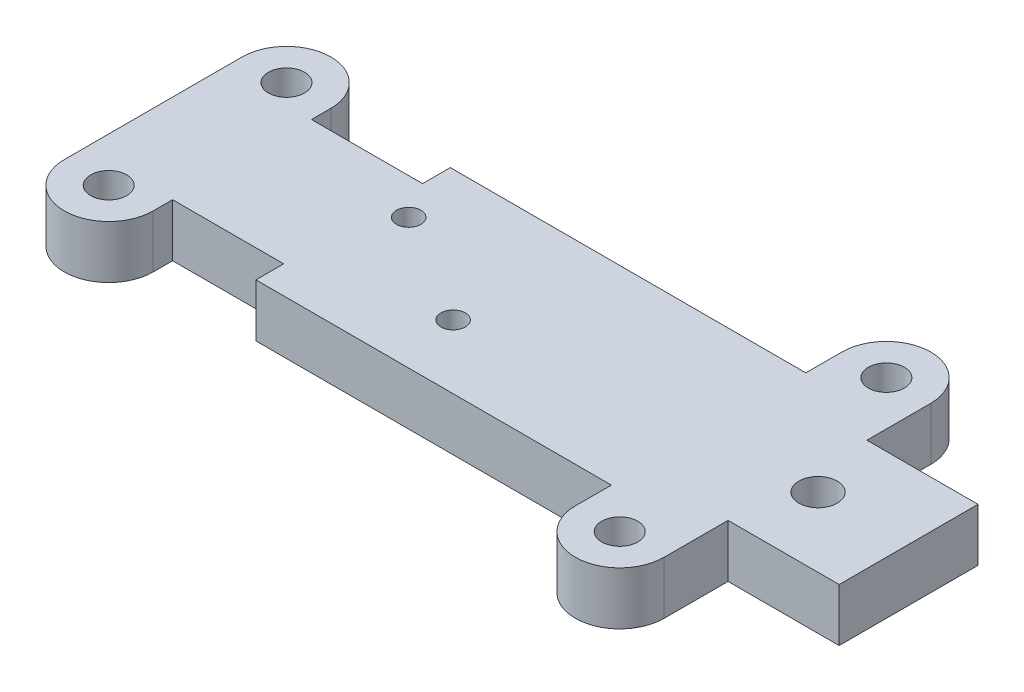
SolidWorks part; units mm, degrees
ref_plane "Front Plane" through (0, 0, 0) normal (0, 0, 1) x (1, 0, 0)
ref_plane "Top Plane" through (0, 0, 0) normal (0, 1, 0) x (1, 0, 0)
ref_plane "Right Plane" through (0, 0, 0) normal (1, 0, 0) x (0, 0, -1)
sketch "Sketch1" plane through (0, 0, 0) normal (0, 1, 0) x (1, 0, 0)
  line L0 (0, 0) -> (-25, 0) construction
  line L1 (-17, 6.25) -> (-17, 8)
  line L2 (-25, 8) -> (-25, 0)
  line L3 (25, 8.75) -> (25, 12)
  line L5 (-7, 8.75) -> (25, 8.75)
  line L6 (43, 6.25) -> (43, 0)
  line L7 (-17, 6.25) -> (-7, 6.25)
  line L8 (-7, 8.75) -> (-7, 6.25)
  line L9 (33, 6.25) -> (43, 6.25)
  line L10 (33, 6.25) -> (33, 12)
  line L11 (43, 0) -> (-25, 0)
  circle A0 centre (5, -3) radius 1.1 construction
  circle A1 centre (-5, 3) radius 1.1 construction
  arc A2 (-17, 8) -> (-25, 8) centre (-21, 8) ccw
  circle A3 centre (-21, 8) radius 1.625
  arc A4 (25, 12) -> (33, 12) centre (29, 12) cw
  circle A5 centre (29, 12) radius 1.625
  dimension "D5" = 2.2
  dimension "D7" = 4
  dimension "D10" = 3.25
  dimension "D1" = 3
  dimension "D2" = 3
  dimension "D3" = 5
  dimension "D4" = 5
  dimension "D6" = 10
  dimension "D8" = 8
  dimension "D9" = 2.5
  dimension "D11" = 40
  dimension "D12" = 7
  dimension "D13" = 6.25
  dimension "D14" = 10
  dimension "D15" = 12
extrude "Boss-Extrude1" add sketch "Sketch1" along normal blind 4.7625
mirror "Mirror1" about plane through (0, 0, 0) normal (0, 0, 1) of "Boss-Extrude1"
sketch "Sketch6" plane through (0, 4.7625, 0) normal (0, 1, 0) x (1, 0, 0)
  circle A0 centre (5, -3) radius 1.1
  circle A1 centre (-5, 3) radius 1.1
  point P7 (9.5949, -3.2775)
  dimension "D1" = 2.2
  dimension "D2" = 3
  dimension "D3" = 3
  dimension "D4" = 5
  dimension "D5" = 5
extrude "Cut-Extrude3" cut sketch "Sketch6" against normal through all
hole_wizard "#8-32 Tapped Hole1" positions "Sketch4" profile "Sketch3" tap size "#8-32" standard "Ansi Inch"
sketch "Sketch4" plane through (0, 4.7625, 0) normal (0, 1, 0) x (-1, 0, 0)
  point P0 (-34.85, 0)
  dimension "D1" = 34.85
sketch "Sketch3" plane through (34.85, 4.7625, 0) normal (1, 0, 0) x (0, 0, 1)
  line L0 (0, 0) -> (0, 13.3278)
  line L1 (0, 13.3278) -> (1.7272, 12.29)
  line L2 (1.7272, 12.29) -> (1.7272, 0)
  line L5 (1.7272, 0) -> (0, 0)
  line L10 (0, 13.3278) -> (-1.7272, 12.29) construction
  line L11 (0, -6.35) -> (0, 107.95) construction
  dimension "Tap Drill Dia." = 3.4544
  dimension "Tap Drill Depth" = 12.29
  dimension "Drill Angle" = 118
cosmetic thread "Hole Thread1" parameters "D1"=3.175, "D2"=4.1656
